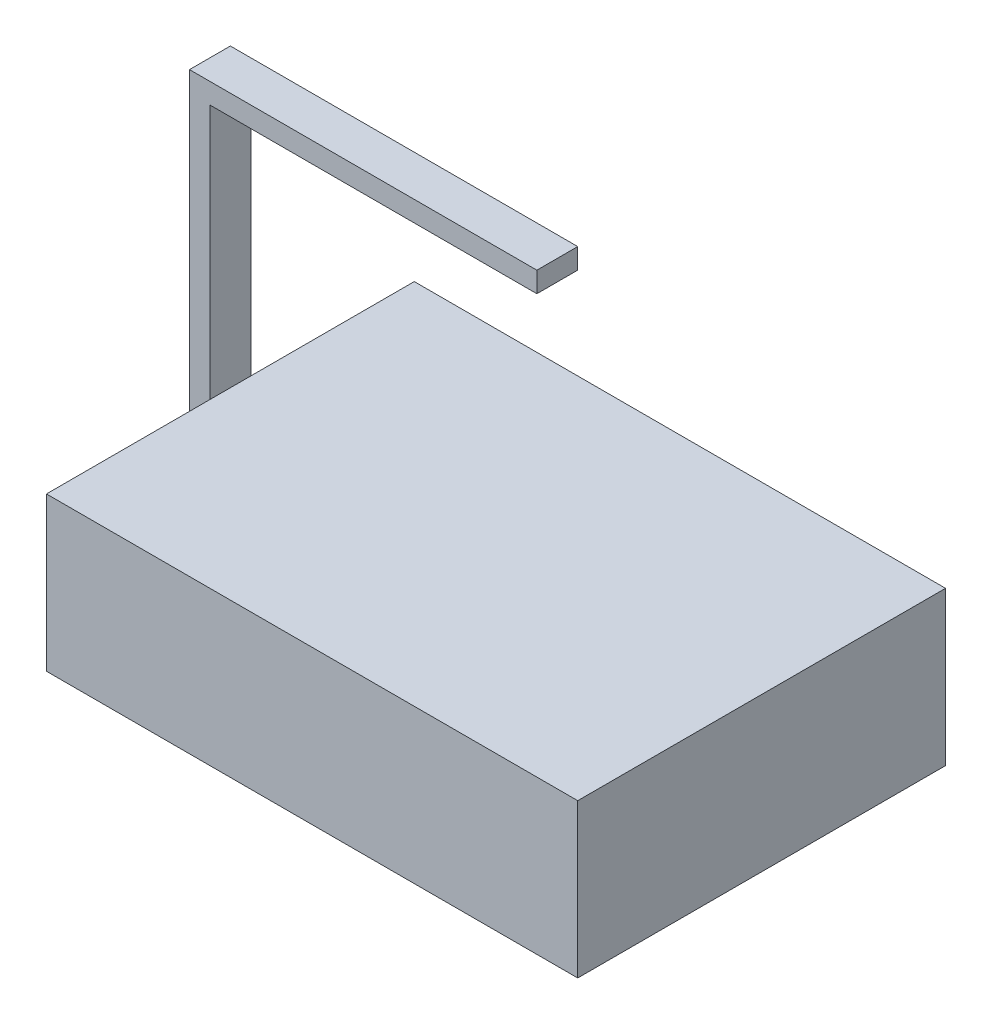
SolidWorks part; units mm, degrees
ref_plane "Front" through (0, 0, 0) normal (0, 0, 1) x (1, 0, 0)
ref_plane "Top" through (0, 0, 0) normal (0, 1, 0) x (1, 0, 0)
ref_plane "Right" through (0, 0, 0) normal (1, 0, 0) x (0, 0, -1)
sketch "Sketch1" plane through (0, 0, 0) normal (0, 1, 0) x (1, 0, 0)
  line L1 (0, 0) -> (130, 0)
  line L2 (0, 0) -> (0, -90)
  line L3 (0, -90) -> (130, -90)
  line L4 (130, 0) -> (130, -90)
  dimension "D1" = 90
  dimension "D2" = 130
extrude "Boss-Extrude1" add sketch "Sketch1" along normal blind 37.58
sketch "Sketch2" plane through (0, 0, 0) normal (-1, 0, 0) x (0, 0, 1)
  line L0 (0, 0) -> (90, 0) construction
  line L1 (40, 0) -> (50, 0)
  line L2 (40, 0) -> (40, 100)
  line L3 (40, 100) -> (50, 100)
  line L4 (50, 0) -> (50, 100)
  line L5 (0, 37.58) -> (90, 37.58) construction
  point P6 (45, 100)
  point P9 (45, 37.58)
  dimension "D1" = 10
  dimension "D2" = 100
extrude "Boss-Extrude2" add sketch "Sketch2" along normal blind 5
sketch "Sketch3" plane through (0, 100, 0) normal (0, 1, 0) x (1, 0, 0)
  line L0 (-5, -50) -> (0, -50) construction
  line L1 (-5, -40) -> (80, -40)
  line L2 (-5, -40) -> (-5, -50)
  line L3 (-5, -50) -> (80, -50)
  line L4 (80, -40) -> (80, -50)
  dimension "D1" = 85
extrude "Boss-Extrude3" add sketch "Sketch3" along normal blind 5
